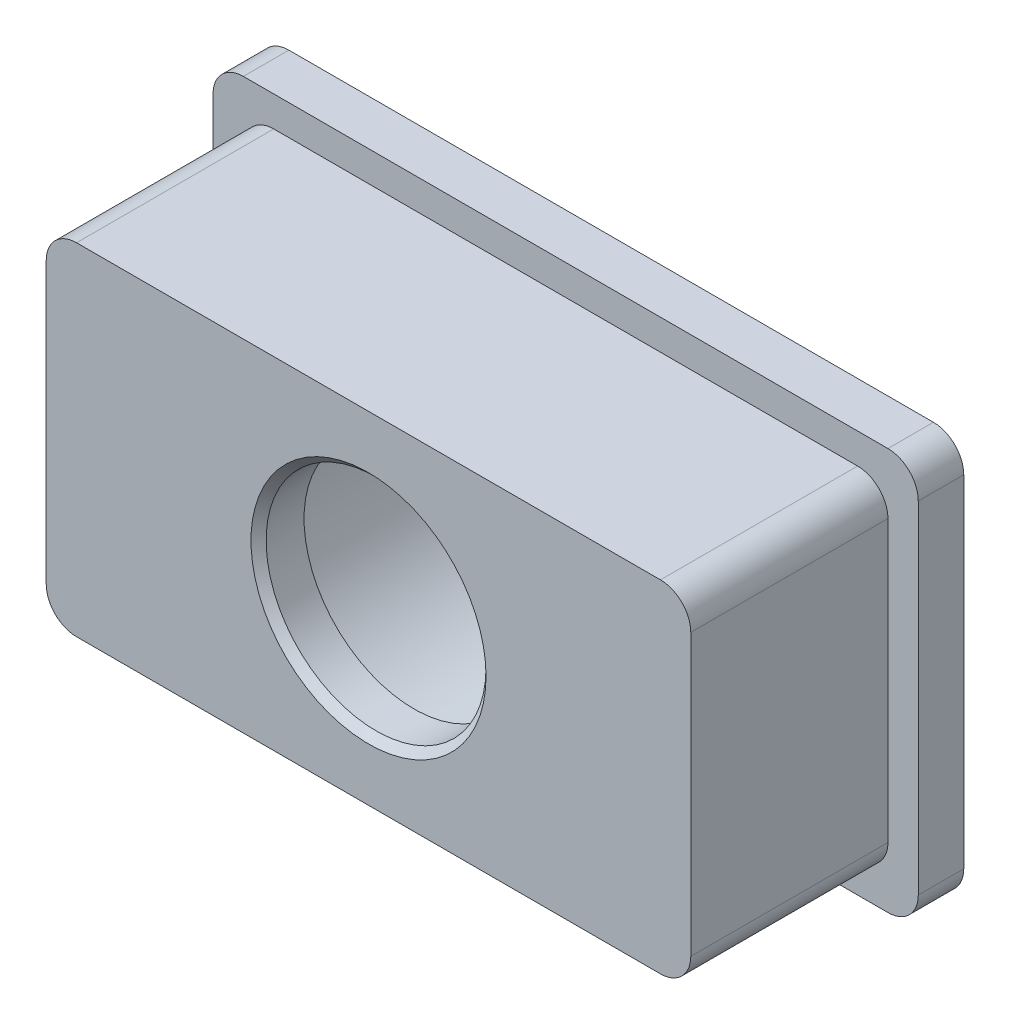
SolidWorks part; units mm, degrees
ref_plane "Front Plane" through (0, 0, 0) normal (0, 0, 1) x (1, 0, 0)
ref_plane "Top Plane" through (0, 0, 0) normal (0, 1, 0) x (1, 0, 0)
ref_plane "Right Plane" through (0, 0, 0) normal (1, 0, 0) x (0, 0, -1)
sketch "Sketch1" plane through (0, 0, 0) normal (0, 0, 1) x (1, 0, 0)
  line L1 (-21.25, 11.25) -> (21.25, 11.25)
  line L2 (-21.25, 11.25) -> (-21.25, -11.25)
  line L3 (-21.25, -11.25) -> (21.25, -11.25)
  line L4 (21.25, 11.25) -> (21.25, -11.25)
  line L5 (-21.25, 11.25) -> (21.25, -11.25) construction
  line L6 (-21.25, -11.25) -> (21.25, 11.25) construction
  point P0 (0, 0)
  dimension "D1" = 42.5
  dimension "D2" = 22.5
extrude "Boss-Extrude1" add sketch "Sketch1" along normal blind 13
shell "Shell1" [suppressed] thickness 3
sketch "Sketch2" plane through (0, 0, 0) normal (0, 0, -1) x (-1, 0, 0)
  line L0 (-21.25, 11.25) -> (21.25, 11.25) construction
  line L1 (-23.25, 13.25) -> (23.25, 13.25)
  line L2 (-23.25, 13.25) -> (-23.25, -13.25)
  line L3 (-23.25, -13.25) -> (23.25, -13.25)
  line L4 (23.25, 13.25) -> (23.25, -13.25)
  line L5 (-23.25, 13.25) -> (23.25, -13.25) construction
  line L6 (-23.25, -13.25) -> (23.25, 13.25) construction
  line L7 (21.25, 11.25) -> (21.25, -11.25) construction
  point P0 (0, 0)
  dimension "D1" = 2
  dimension "D2" = 2
extrude "Boss-Extrude2" add sketch "Sketch2" along normal blind 3
sketch "Sketch3" plane through (0, 0, 13) normal (0, 0, 1) x (1, 0, 0)
  line L8 (18.25, -8.25) -> (18.25, 8.25)
  line L9 (18.25, 8.25) -> (-18.25, 8.25)
  line L10 (-18.25, 8.25) -> (-18.25, -8.25)
  line L11 (-18.25, -8.25) -> (18.25, -8.25)
  line L12 (18.25, -8.25) -> (18.25, 8.25)
  line L13 (18.25, 8.25) -> (-18.25, 8.25)
  line L14 (-18.25, 8.25) -> (-18.25, -8.25)
  line L15 (-18.25, -8.25) -> (18.25, -8.25)
  dimension "D1" = 3
extrude "Cut-Extrude1" [suppressed] cut sketch "Sketch3" against normal offset from surface (13 mm away) 3
sketch "Sketch5" plane through (0, 0, -3) normal (0, 0, -1) x (-1, 0, 0)
  circle A0 centre (0, 0) radius 60
  dimension "D1" = 120
extrude "Boss-Extrude3" [suppressed] add sketch "Sketch5" along normal blind 3 contours A0
sketch "Sketch6" plane through (0, 0, -3) normal (0, 0, -1) x (-1, 0, 0)
  circle A0 centre (0, 0) radius 10.25
  dimension "D1" = 20.5
extrude "Cut-Extrude2" cut sketch "Sketch6" against normal up to next contours A0
sketch "Sketch7" plane through (0, 0, 13) normal (0, 0, 1) x (1, 0, 0)
  circle A0 centre (0, 0) radius 10.25
  circle A1 centre (0, 0) radius 10.25 construction
  circle A2 centre (0, 0) radius 7.25
  dimension "D1" = 3
extrude "Boss-Extrude4" add sketch "Sketch7" against normal blind 3
shell "Shell2" [suppressed] thickness 3
fillet "Fillet1" radius 2 8 edges at (-23.25, -13.25, -1.5) (-23.25, 13.25, -1.5) (23.25, -13.25, -1.5) (23.25, 13.25, -1.5) (21.25, 11.25, 6.5) (-21.25, 11.25, 6.5) (-21.25, -11.25, 6.5) (21.25, -11.25, 6.5)
chamfer "Chamfer1" distance 0.5 angle 45 2 edges at (7.25, 0, 13) (-10.25, 0, -3)
